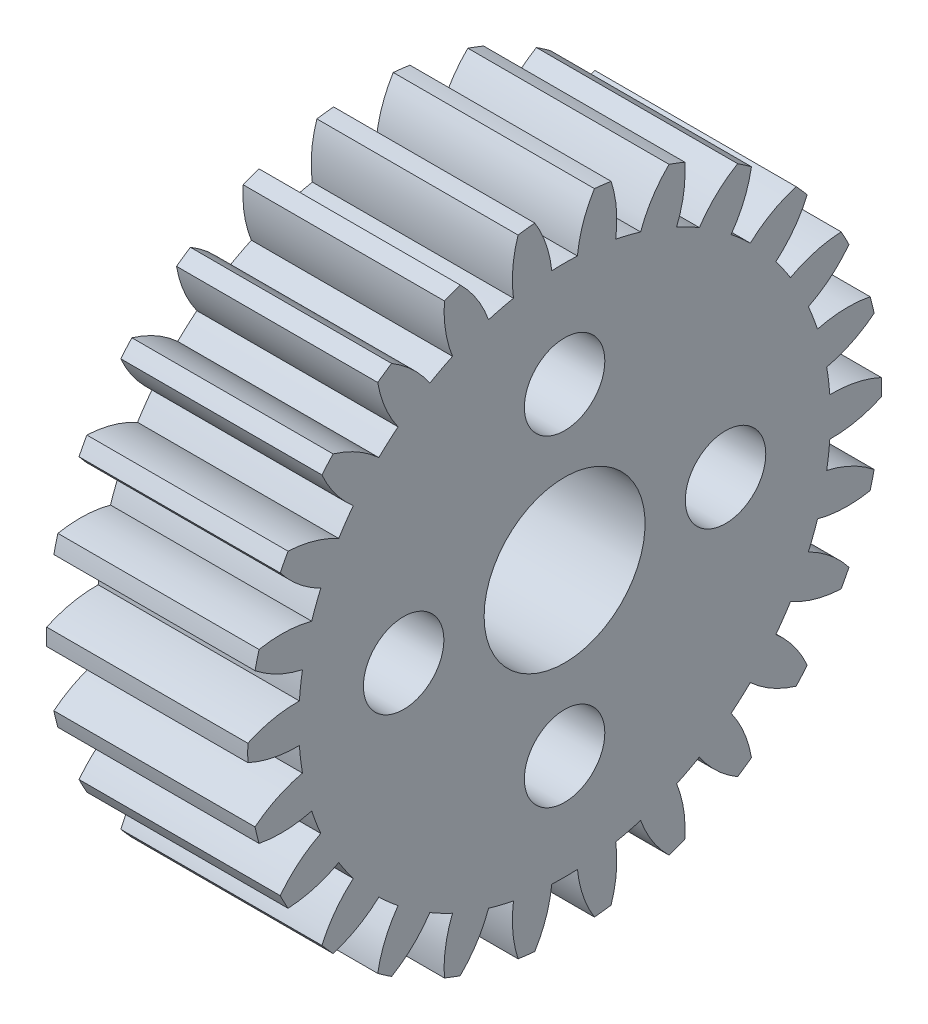
SolidWorks part; units mm, degrees
ref_plane "Plane1" through (0, 0, 0) normal (0, 0, 1) x (1, 0, 0)
ref_plane "Plane2" through (0, 0, 0) normal (0, 1, 0) x (1, 0, 0)
ref_plane "Plane3" through (0, 0, 0) normal (1, 0, 0) x (0, 0, -1)
sketch "HoldingSke" plane through (0, 0, 0) normal (0, 1, 0) x (1, 0, 0)
  line L0 (0, 0) -> (0.7989, -0.3897)
  line L1 (-15, 0) -> (100, 0) construction
  line L2 (0, 0) -> (-2.1039, 2.3779)
  line L3 (0, 0) -> (-11.863, 4.5341)
  line L4 (0, 0) -> (7.762, 3.7858)
  line L5 (0, 0) -> (-46.8476, -17.4728)
  line L6 (0, 0) -> (-8.2896, -5.593)
  line L7 (-2.1039, 2.3779) -> (8.6586, 51.2059)
  line L8 (-76.2, 54.61) -> (-74.8, 54.61)
  line L9 (-67.7845, 28.3722) -> (-49.3413, 33.142)
  line L10 (-76.2, 71.12) -> (104.1128, 71.12)
  line L11 (0, 0) -> (-10, 0)
  line L12 (-76.2, 101.6) -> (-76.158, 101.6)
  line L13 (24.9733, 27.94) -> (52.9518, 28.4284)
  line L14 (24.9733, 27.94) -> (24.9743, 27.94)
  line L15 (24.9733, 27.94) -> (100.4006, 29.5858)
  line L16 (-63.627, -1.125) -> (-12.827, -1.125)
  circle A0 centre (0, 0) radius 4
  circle A1 centre (0, 0) radius 13.2177
  circle A2 centre (0, 0) radius 37.5
  circle A3 centre (0, 0) radius 4
  dimension "MHD" = 26.4355
  dimension "Hub_dia" = 75
  dimension "Bore" = 8
  dimension "MBD" = 8
  dimension "Num_teeth" = 26
  dimension "Pitch" = 0.8889
  dimension "Overall_len" = 50
  dimension "Show_teeth" = 26
  dimension "Thickness" = 10
  dimension "OAL" = 50.0001
  dimension "T_dim" = 1.4
  dimension "Ap" = 14.5
  dimension "H" = 19.05
  dimension "Pitch_radius" = 180.3128
  dimension "Width" = 10
  dimension "Backlash" = 0.042
  dimension "Addendum_fac" = 1
  dimension "Dedendum_fac" = 1.25
  dimension "Clearance_fac" = 0.25
  dimension "Dedendum_add" = 0.001
  dimension "Module" = 1.125
sketch "BasProSke" plane through (0, 0, 0) normal (0, 1, 0) x (1, 0, 0)
  line L0 (-10, 0) -> (60, 0) construction
  line L1 (0, 0) -> (0, 15.75)
  line L2 (0, 0) -> (10, 0)
  line L3 (10, 0) -> (10, 15.75)
  line L4 (10, 15.75) -> (0, 15.75)
  dimension "Thickness" = 10
  dimension "Diameter" = 31.5
revolve "Base-Revolve" add sketch "BasProSke" angle 360 about L0
sketch "TooCutSke" plane through (0, 0, 0) normal (1, 0, 0) x (0, 0, -1)
  line L1 (0, 0) -> (0, 107) construction
  line L2 (0, 0) -> (-0.9565, 14.5937) construction
  line L3 (0, 0) -> (-3.5203, 28.9922) construction
  line L4 (-0.9565, 14.5937) -> (-1.7601, 14.4961) construction
  arc A0 (0.6377, 13.2024) -> (-0.6377, 13.2024) centre (0, 0) ccw
  arc A1 (1.4975, 15.7042) -> (-1.4975, 15.7042) centre (0, 0) ccw
  circle A2 centre (0, 0) radius 14.625 construction
  circle A3 centre (0, 0) radius 14.1592 construction
  arc A4 (-0.6377, 13.2024) -> (-1.4975, 15.7042) centre (-6.4568, 12.6013) ccw
  arc A5 (1.4975, 15.7042) -> (0.6377, 13.2024) centre (6.4568, 12.6013) ccw
  dimension "Root_dia" = 26.4355
  dimension "Overcut_dia" = 31.5508
  dimension "Pitch_dia" = 29.25
  dimension "Base_dia" = 28.3183
  dimension "Flank_rad" = 5.85
  dimension "Half_ang" = 6.923
  dimension "Half_CT" = 0.8095
extrude "ToothCut" cut sketch "TooCutSke" along normal through all
fillet "Breaks" [suppressed] radius 0.0225
fillet "RootFillets" [suppressed] radius 0.2822
pattern_circular "TeethCuts" count 26 every 13.846 about axis through (-10, 0, 0) along (1, 0, 0) of "ToothCut", "RootFillets", "Breaks"
sketch "HubNeaOneSke" plane through (0, 0, 0) normal (-1, 0, 0) x (0, 0, 1)
  circle A0 centre (0, 0) radius 13.2177
  dimension "Diameter" = 26.4355
extrude "HubNearOne" [suppressed] add sketch "HubNeaOneSke" along normal blind 40.0001
sketch "HubNeaBotSke" plane through (0, 0, 0) normal (-1, 0, 0) x (0, 0, 1)
  circle A0 centre (0, 0) radius 13.2177
  dimension "Diameter" = 26.4355
extrude "HubNearBoth" [suppressed] add sketch "HubNeaBotSke" along normal blind 20
ref_plane "FarPln" through (10, 0, 0) normal (1, 0, 0) x (0, 0, -1)
sketch "HubFarSke" plane through (10, 0, 0) normal (1, 0, 0) x (0, 0, -1)
  circle A0 centre (0, 0) radius 13.2177
  dimension "Diameter" = 26.4355
extrude "HubFar" [suppressed] add sketch "HubFarSke" along normal blind 20
sketch "BorSke" plane through (0, 0, 0) normal (1, 0, 0) x (0, 0, -1)
  circle A0 centre (0, 0) radius 4
  dimension "Diameter" = 8
extrude "Bore" cut sketch "BorSke" along normal mid plane 100.0001
sketch "KeySke" plane through (0, 0, 0) normal (1, 0, 0) x (0, 0, -1)
  line L0 (-1, 0) -> (-1, 5.4)
  line L1 (-1, 5.4) -> (1, 5.4)
  line L2 (1, 5.4) -> (1, 0)
  line L3 (0, 0) -> (0, 34) construction
  line L4 (-1, 0) -> (1, 0)
  dimension "Offset" = 5.4
  dimension "Width" = 2
extrude "Keyway" [suppressed] cut sketch "KeySke" along normal mid plane 100.0001
pattern_circular "Keyway2" [suppressed] count 2 every 90 about axis through (-10, 0, 0) along (1, 0, 0)
sketch "Sketch1" plane through (10, 0, 0) normal (1, 0, 0) x (0, 0, -1)
  line L0 (0, 12.6831) -> (0, -11.6055) construction
  line L1 (-12.653, 0) -> (13.7286, 0) construction
  circle A0 centre (0, 0) radius 8
  circle A1 centre (0, 0) radius 4 construction
  circle A2 centre (8, 0) radius 2
  circle A3 centre (0, -8) radius 2
  circle A4 centre (-8, 0) radius 2
  circle A5 centre (0, 8) radius 2
  point P21 (0, 0)
  dimension "D1" = 16
  dimension "D2" = 4
  dimension "D3" = 4
extrude "Cut-Extrude2" cut sketch "Sketch1" against normal blind 5 contours A4 | A5 | A2 | A3
sketch "Sketch2" plane through (10, 0, 0) normal (1, 0, 0) x (0, 0, -1)
  line L0 (0, 12.6831) -> (0, -11.6055) construction
  line L1 (-12.653, 0) -> (13.7286, 0) construction
  line L2 (0, 12.6831) -> (0, -11.6055)
  line L3 (-12.653, 0) -> (13.7286, 0)
  circle A0 centre (0, 0) radius 8 construction
  circle A1 centre (0, 0) radius 8
  circle A2 centre (8, 0) radius 1
  circle A3 centre (0, -8) radius 1
  circle A4 centre (-8, 0) radius 1
  circle A5 centre (0, 8) radius 1
  point P19 (0, 0)
  dimension "D1" = 2
  dimension "D3" = 16
  dimension "D2" = 4
extrude "Cut-Extrude3" cut sketch "Sketch2" against normal up to surface (10 mm away) contours A4 | A5 | A2 | A3 up to face at (0, 0, -4)
equation "' \"Module@HoldingSke\" = 6.35"
equation "' \"Num_teeth@HoldingSke\" = 12"
equation "' \"Ap@HoldingSke\" =  20"
equation "' \"Ap@HoldingSke\" = 20"
equation "' \"Width@HoldingSke\" = 0.5 * 25.4"
equation "' \"Hub_dia@HoldingSke\"= 1 * 25.4"
equation "' \"Hub_dia@HoldingSke\" = 1 * 25.4"
equation "' \"Overall_len@HoldingSke\" = 1.0 * 25.4"
equation "' \"Bore@HoldingSke\" = 0.75 * 25.4"
equation "' \"T_dim@HoldingSke\" = 0.1 * 25.4"
equation "' \"Width@KeySke\" = 0.25 * 25.4"
equation "' \"Show_teeth@HoldingSke\" = 13"
equation "' \"Backlash@HoldingSke\" = 0.009 * 25.4"
equation "' \"Addendum_fac@HoldingSke\" = 1.0"
equation "' \"Dedendum_fac@HoldingSke\" = 1.25"
equation "' \"Dedendum_add@HoldingSke\" = 0.00005 * 25.4"
equation "' \"Clearance_fac@HoldingSke\" = 0.25"
equation "\"Pitch@HoldingSke\" = 1 / \"Module@HoldingSke\""
equation "\"Overcut_dia@TooCutSke\" = (\"Num_teeth@HoldingSke\" + 2 * \"Addendum_fac@HoldingSke\") / \"Pitch@HoldingSke\" + 0.002 * 25.4"
equation "\"Pitch_dia@TooCutSke\" = \"Num_teeth@HoldingSke\" / \"Pitch@HoldingSke\""
equation "\"Base_dia@TooCutSke\" = \"Num_teeth@HoldingSke\" / \"Pitch@HoldingSke\" * cos((\"Ap@HoldingSke\"  * 3.14159265 / 180))"
equation "\"Root_dia@TooCutSke\" = (\"Num_teeth@HoldingSke\" + 2) / \"Pitch@HoldingSke\" - 2 * (\"Addendum_fac@HoldingSke\" + \"Dedendum_fac@HoldingSke\") / \"Pitch@HoldingSke\" - \"Dedendum_add@HoldingSke\" * 2"
equation "\"Half_ang@TooCutSke\" = 180 / \"Num_teeth@HoldingSke\""
equation "\"Half_CT@TooCutSke\" = \"Num_teeth@HoldingSke\" / \"Pitch@HoldingSke\" * sin((3.14159265 / 2 / \"Num_teeth@HoldingSke\")) / 2 - 7 * \"Backlash@HoldingSke\" / 4"
equation "\"Flank_rad@TooCutSke\" = \"Num_teeth@HoldingSke\" / \"Pitch@HoldingSke\" / 5"
equation "\"Radius@RootFillets\" = \"Clearance_fac@HoldingSke\" / \"Pitch@HoldingSke\" + \"Dedendum_add@HoldingSke\""
equation "\"Break_rad@Breaks\" = 0.02 / \"Pitch@HoldingSke\""
equation "\"Thickness@HoldingSke\" = \"Width@HoldingSke\""
equation "\"OAL@HoldingSke\" = \"Thickness@HoldingSke\""
equation "\"MHD@HoldingSke\" = (\"Num_teeth@HoldingSke\" + 2) / \"Pitch@HoldingSke\" - 2 * (\"Addendum_fac@HoldingSke\" + \"Dedendum_fac@HoldingSke\")  / \"Pitch@HoldingSke\" - \"Dedendum_add@HoldingSke\" * 2"
equation "\"MBD@HoldingSke\" = (\"Num_teeth@HoldingSke\" + 2) / \"Pitch@HoldingSke\" - 2 * (\"Addendum_fac@HoldingSke\" + \"Dedendum_fac@HoldingSke\")  / \"Pitch@HoldingSke\" - \"Dedendum_add@HoldingSke\" * 2 - 0.002 * 25.4"
equation "\"MHD@HoldingSke\" = ((sgn( \"MHD@HoldingSke\" - \"Hub_dia@HoldingSke\" )-1)*( \"MHD@HoldingSke\" - \"Hub_dia@HoldingSke\" ))/-2+ \"Hub_dia@HoldingSke\""
equation "\"MBD@HoldingSke\" = ((sgn( \"MBD@HoldingSke\" - \"Bore@HoldingSke\" )-1)*( \"MBD@HoldingSke\" - \"Bore@HoldingSke\" ))/-2+ \"Bore@HoldingSke\""
equation "\"OAL@HoldingSke\" = ((sgn( \"OAL@HoldingSke\" - \"Overall_len@HoldingSke\" )+1)*( \"OAL@HoldingSke\" - \"Overall_len@HoldingSke\" ))/2 + \"Overall_len@HoldingSke\" + 0.000002 * 25.4"
equation "\"Num_teeth@TeethCuts\" = int( \"Show_teeth@HoldingSke\" ) + 1"
equation "\"Num_teeth@TeethCuts\" = ((sgn( \"Num_teeth@TeethCuts\" - \"Num_teeth@HoldingSke\" )-1)*( \"Num_teeth@TeethCuts\" - \"Num_teeth@HoldingSke\" ))/-2+ \"Num_teeth@HoldingSke\""
equation "\"Num_teeth@TeethCuts\" = ((sgn( \"Num_teeth@TeethCuts\" - 2.0)+1)*( \"Num_teeth@TeethCuts\" - 2.0))/2 +2.0"
equation "\"Angle@TeethCuts\" = 360.0 / \"Num_teeth@HoldingSke\""
equation "\"Diameter@BasProSke\" = (\"Num_teeth@HoldingSke\" + 2 * \"Addendum_fac@HoldingSke\") / \"Pitch@HoldingSke\""
equation "\"Thickness@BasProSke\"  = \"Thickness@HoldingSke\""
equation "' \"Fillet_rad@BasProSke\" =  \"Thickness@HoldingSke\" * 0.05"
equation "' \"Fillet_rad@BasProSke\" = \"Thickness@HoldingSke\" * 0.05"
equation "\"MHD@HoldingSke\" = ((sgn( \"MHD@HoldingSke\" - \"Root_dia@TooCutSke\" )-1)*( \"MHD@HoldingSke\" - \"Root_dia@TooCutSke\" ))/-2+ \"Root_dia@TooCutSke\""
equation "\"Diameter@HubNeaOneSke\" = \"MHD@HoldingSke\""
equation "\"Length@HubNearOne\" = \"OAL@HoldingSke\" - \"Thickness@BasProSke\""
equation "\"Diameter@HubNeaBotSke\" = \"MHD@HoldingSke\""
equation "\"Length@HubNearBoth\" = ( \"OAL@HoldingSke\" - \"Thickness@BasProSke\" ) / 2.0"
equation "\"Thickness@FarPln\" = \"Thickness@BasProSke\""
equation "\"Diameter@HubFarSke\" = \"MHD@HoldingSke\""
equation "\"Length@HubFar\" = ( \"OAL@HoldingSke\" - \"Thickness@BasProSke\" ) / 2.0"
equation "\"Diameter@BorSke\" = \"MBD@HoldingSke\""
equation "\"D1@Bore\" = \"OAL@HoldingSke\" * 2.0"
equation "\"D1@Keyway\" = \"OAL@HoldingSke\" * 2.0"
equation "\"Offset@KeySke\" = \"T_dim@HoldingSke\" + \"MBD@HoldingSke\" / 2.0"
